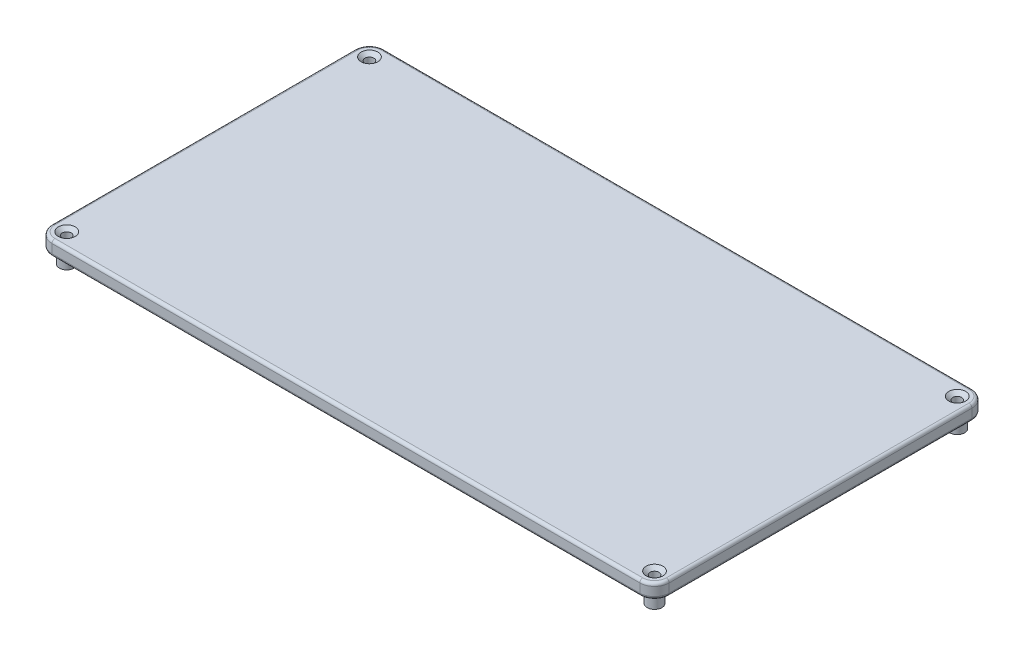
SolidWorks part; units mm, degrees
ref_plane "Front Plane" through (0, 0, 0) normal (0, 0, 1) x (1, 0, 0)
ref_plane "Top Plane" through (0, 0, 0) normal (0, 1, 0) x (1, 0, 0)
ref_plane "Right Plane" through (0, 0, 0) normal (1, 0, 0) x (0, 0, -1)
sketch "Sketch1" plane through (0, 0, 0) normal (0, 1, 0) x (1, 0, 0)
  line L1 (-105, -56.5) -> (105, -56.5)
  line L2 (-105, -56.5) -> (-105, 56.5)
  line L3 (-105, 56.5) -> (105, 56.5)
  line L4 (105, -56.5) -> (105, 56.5)
  line L5 (-105, -56.5) -> (105, 56.5) construction
  line L6 (-105, 56.5) -> (105, -56.5) construction
  point P0 (0, 0)
  dimension "D1" = 210
  dimension "D2" = 113
extrude "Boss-Extrude1" add sketch "Sketch1" along normal blind 5
fillet "Fillet1" radius 5 4 edges at (-105, 2.5, -56.5) (-105, 2.5, 56.5) (105, 2.5, 56.5) (105, 2.5, -56.5)
fillet "Fillet2" radius 1 16 edges at (-103.5355, 5, 55.0355) (-105, 5, 0) (-103.5355, 5, -55.0355) (0, 5, -56.5) (103.5355, 5, -55.0355) (105, 5, 0) (103.5355, 5, 55.0355) (-103.5355, 0, 55.0355) (-105, 0, 0) (-103.5355, 0, -55.0355) (0, 0, -56.5) (103.5355, 0, -55.0355) (105, 0, 0) (103.5355, 0, 55.0355) (0, 5, 56.5) (0, 0, 56.5)
hole_wizard "CSK for #4 Flat Head Machine Screw (100)1" positions "Sketch5" profile "Sketch6" countersink size "#4" standard "ANSI Inch" end condition through all
sketch "Sketch5" plane through (0, 5, 0) normal (0, 1, 0) x (1, 0, 0)
  point P0 (-100, -51.5)
  point P3 (100, 51.5)
  point P6 (100, -51.5)
  point P9 (-100, 51.5)
sketch "Sketch6" plane through (-100, 5, 51.5) normal (1, 0, 0) x (0, 0, 1)
  line L0 (0, 0) -> (0, 5)
  line L1 (0, 5) -> (1.4732, 5)
  line L2 (1.4732, 5) -> (1.4732, 1.1616)
  line L3 (1.4732, 1.1616) -> (2.8575, 0)
  line L5 (2.8575, 0) -> (0, 0)
  line L6 (-1.4732, 1.1616) -> (-2.8575, 0) construction
  line L11 (0, -6.35) -> (0, 107.95) construction
  dimension "Thru Hole Dia." = 2.9464
  dimension "Thru Hole Depth" = 5
  dimension "Near C'Sink Dia." = 5.715
  dimension "Near C'Sink Angle" = 100
sketch "Sketch8" plane through (0, 0, 0) normal (0, -1, 0) x (1, 0, 0)
  circle A0 centre (-100, 51.5) radius 2.4732
extrude "Boss-Extrude2" add sketch "Sketch8" along normal blind 4.525
sketch "Sketch10" plane through (0, -4.525, 0) normal (0, -1, 0) x (1, 0, 0)
  circle A0 centre (-100, 51.5) radius 1.525
extrude "Cut-Extrude1" cut sketch "Sketch10" against normal through all both and the other way through all
sketch "Sketch11" plane through (0, 0, 0) normal (0, -1, 0) x (1, 0, 0)
  circle A0 centre (-100, -51.5) radius 2.525
extrude "Boss-Extrude3" add sketch "Sketch11" along normal blind 4.525
sketch "Sketch14" plane through (0, -4.525, 0) normal (0, -1, 0) x (1, 0, 0)
  circle A0 centre (-100, -51.5) radius 1.525
extrude "Cut-Extrude2" cut sketch "Sketch14" against normal through all
sketch "Sketch15" plane through (0, 0, 0) normal (0, -1, 0) x (1, 0, 0)
  circle A0 centre (100, 51.5) radius 2.525
extrude "Boss-Extrude6" add sketch "Sketch15" along normal blind 4.525
sketch "Sketch16" plane through (0, -4.525, 0) normal (0, -1, 0) x (1, 0, 0)
  circle A0 centre (100, 51.5) radius 1.525
extrude "Cut-Extrude3" cut sketch "Sketch16" against normal through all
sketch "Sketch17" plane through (0, 0, 0) normal (0, -1, 0) x (1, 0, 0)
  circle A0 centre (100, -51.5) radius 2.525
extrude "Boss-Extrude7" add sketch "Sketch17" along normal blind 4.525
sketch "Sketch18" plane through (0, -4.525, 0) normal (0, -1, 0) x (1, 0, 0)
  circle A0 centre (100, -51.5) radius 1.525
extrude "Cut-Extrude4" cut sketch "Sketch18" against normal through all
